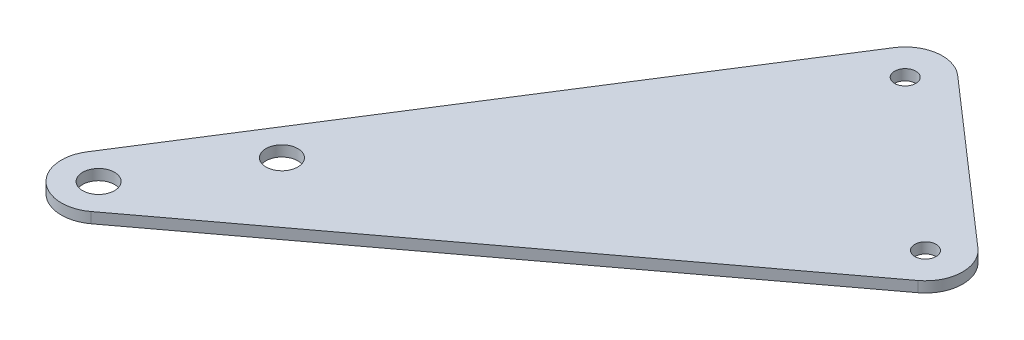
SolidWorks part; units mm, degrees
material "7075-O (SS)"
ref_plane "Płaszczyzna XY" through (0, 0, 0) normal (0, 0, 1) x (1, 0, 0)
ref_plane "Płaszczyzna XZ" through (0, 0, 0) normal (0, 1, 0) x (1, 0, 0)
ref_plane "Płaszczyzna YZ" through (0, 0, 0) normal (1, 0, 0) x (0, 0, -1)
sketch "Szkic1" plane through (0, 0, 0) normal (0, 1, 0) x (1, 0, 0)
  line L6 (1700.5591, -953.9676) -> (1789.6153, -887.3952)
  line L7 (1790.0287, -876.5162) -> (1759.9008, -850.2044)
  line L8 (1690.4572, -944.611) -> (1749.3854, -851.7269)
  circle A0 centre (1755.2962, -855.4768) radius 2
  circle A1 centre (1785.4242, -881.7886) radius 2
  circle A12 centre (1696.368, -948.361) radius 3
  circle A13 centre (1709.7608, -927.2509) radius 3
  arc A14 (1690.4572, -944.611) -> (1700.5591, -953.9676) centre (1696.368, -948.361) ccw
  arc A15 (1789.6153, -887.3952) -> (1790.0287, -876.5162) centre (1785.4242, -881.7886) ccw
  arc A16 (1759.9008, -850.2044) -> (1749.3854, -851.7269) centre (1755.2962, -855.4768) ccw
  dimension "D1" = 4
  dimension "D2" = 4
  dimension "D3" = 6
  dimension "D4" = 6
  dimension "D5" = 14
  dimension "D6" = 14
  dimension "D7" = 14
extrude "Dodanie-wyciągnięcie1" add sketch "Szkic1" along normal blind 2
